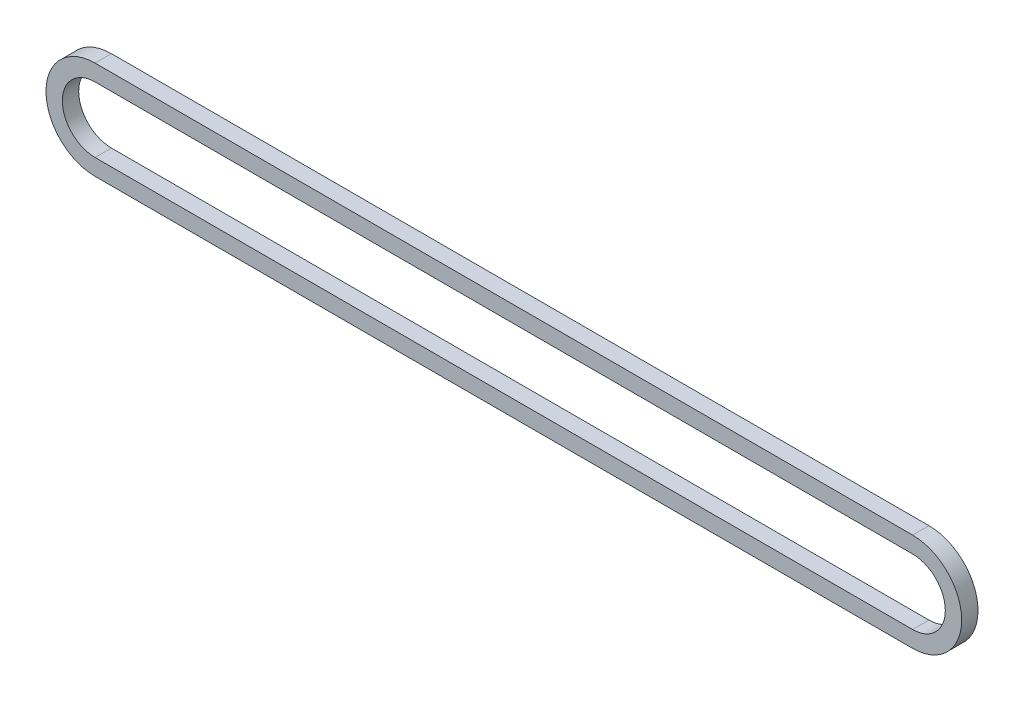
SolidWorks part; units mm, degrees
ref_plane "前视基准面" through (0, 0, 0) normal (0, 0, 1) x (1, 0, 0)
ref_plane "上视基准面" through (0, 0, 0) normal (0, 1, 0) x (1, 0, 0)
ref_plane "右视基准面" through (0, 0, 0) normal (1, 0, 0) x (0, 0, -1)
sketch "草图1" plane through (0, 0, 0) normal (0, 0, 1) x (1, 0, 0)
  line L1 (-52.3146, -4) -> (47.6854, -4)
  line L2 (-52.3146, 4) -> (47.6854, 4)
  line L3 (-52.3146, -6) -> (47.6854, -6)
  line L4 (-52.3146, 6) -> (47.6854, 6)
  arc A0 (47.6854, -4) -> (47.6854, 4) centre (47.6854, 0) ccw
  arc A1 (47.6854, -6) -> (47.6854, 6) centre (47.6854, 0) ccw
  arc A2 (-52.3146, 4) -> (-52.3146, -4) centre (-52.3146, 0) ccw
  arc A3 (-52.3146, 6) -> (-52.3146, -6) centre (-52.3146, 0) ccw
  dimension "D1" = 100
extrude "凸台-拉伸1" add sketch "草图1" along normal blind 2
